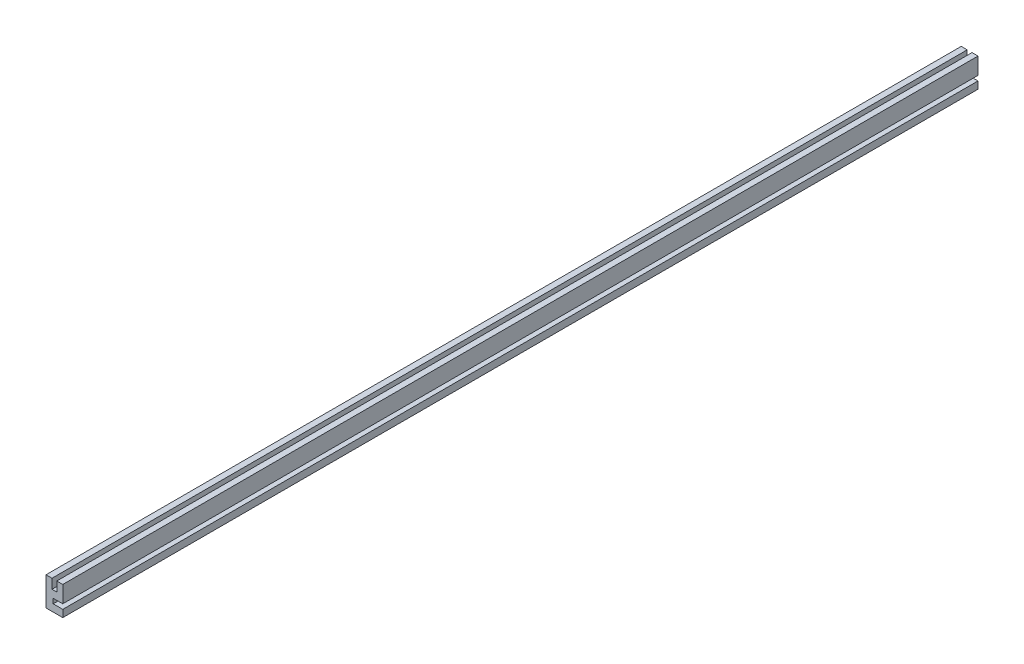
SolidWorks part; units mm, degrees
material "Mahogany"
ref_plane "Front Plane" through (0, 0, 0) normal (0, 0, 1) x (1, 0, 0)
ref_plane "Top Plane" through (0, 0, 0) normal (0, 1, 0) x (1, 0, 0)
ref_plane "Right Plane" through (0, 0, 0) normal (1, 0, 0) x (0, 0, -1)
sketch "Sketch1" plane through (0, 0, 0) normal (0, 0, 1) x (1, 0, 0)
  line L1 (-5.5563, -9.525) -> (5.5562, -9.525)
  line L2 (-5.5563, -9.525) -> (-5.5563, 9.525)
  line L3 (-5.5563, 9.525) -> (5.5562, 9.525)
  line L4 (5.5562, -9.525) -> (5.5562, 9.525)
  line L5 (-5.5563, -9.525) -> (5.5562, 9.525) construction
  line L6 (-5.5563, 9.525) -> (5.5562, -9.525) construction
  point P0 (0, 0)
  dimension "D1" = 11.1125
  dimension "D2" = 19.05
extrude "Wood Strip" add sketch "Sketch1" along normal mid plane 606.425
sketch "Sketch2" plane through (0, 0, 303.2125) normal (0, 0, 1) x (1, 0, 0)
  line L0 (5.5562, 9.525) -> (-5.5563, 9.525) construction
  line L1 (-1.5875, 3.175) -> (1.5875, 3.175)
  line L2 (-1.5875, 3.175) -> (-1.5875, 9.525)
  line L3 (-1.5875, 9.525) -> (1.5875, 9.525)
  line L4 (1.5875, 3.175) -> (1.5875, 9.525)
  line L5 (-1.5875, 3.175) -> (1.5875, 9.525) construction
  line L6 (-1.5875, 9.525) -> (1.5875, 3.175) construction
  point P0 (0, 6.35)
  dimension "D1" = 3.175
  dimension "D2" = 6.35
extrude "Slot for Mounting to Extrusion" cut sketch "Sketch2" against normal through all
sketch "Sketch3" plane through (0, 0, 303.2125) normal (0, 0, 1) x (1, 0, 0)
  line L0 (5.5562, -9.525) -> (5.5562, 9.525) construction
  line L1 (5.5562, -4.7625) -> (-0.7938, -4.7625)
  line L2 (5.5562, -4.7625) -> (5.5562, -1.5875)
  line L3 (5.5562, -1.5875) -> (-0.7938, -1.5875)
  line L4 (-0.7938, -4.7625) -> (-0.7938, -1.5875)
  line L5 (-5.5563, -9.525) -> (5.5562, -9.525) construction
  dimension "D1" = 6.35
  dimension "D2" = 3.175
  dimension "D3" = 4.7625
extrude "Slot for Diffuser" cut sketch "Sketch3" against normal through all
